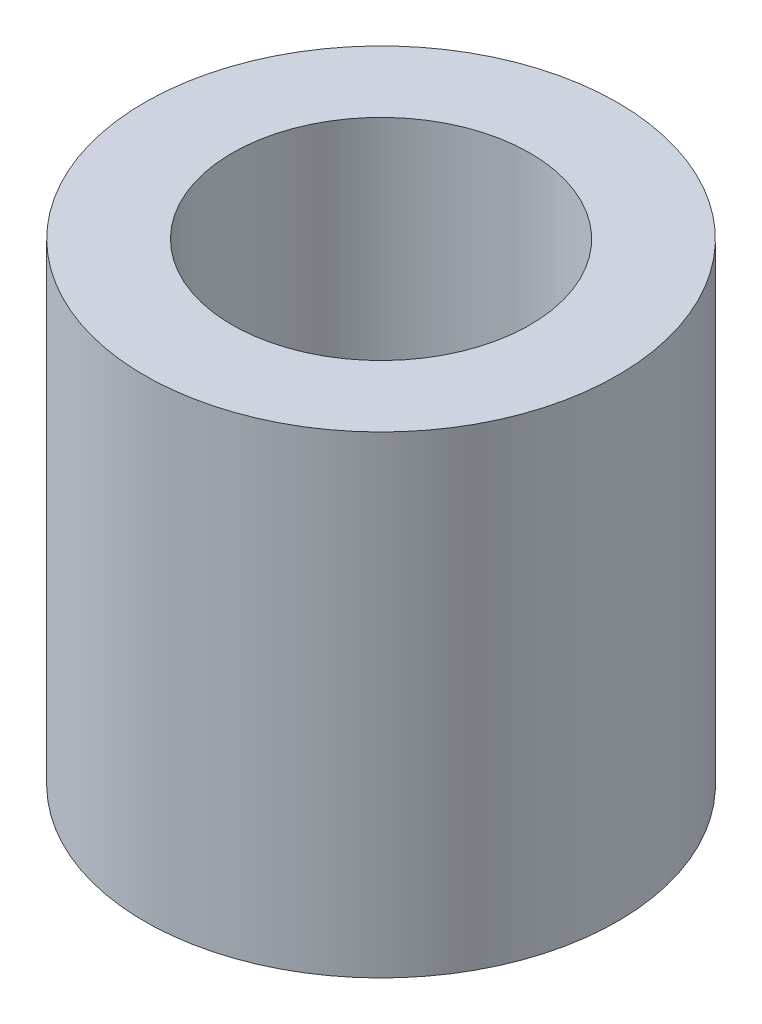
SolidWorks part; units mm, degrees
ref_plane "Front Plane" through (0, 0, 0) normal (0, 0, 1) x (1, 0, 0)
ref_plane "Top Plane" through (0, 0, 0) normal (0, 1, 0) x (1, 0, 0)
ref_plane "Right Plane" through (0, 0, 0) normal (1, 0, 0) x (0, 0, -1)
sketch "Sketch1" plane through (0, 0, 0) normal (0, 0, 1) x (1, 0, 0)
  line L0 (0, 0) -> (0, 6.7287) construction
  line L2 (-2, 0) -> (-3.175, 0)
  line L3 (-2, 0) -> (-2, 6.35)
  line L4 (-2, 6.35) -> (-3.175, 6.35)
  line L5 (-3.175, 0) -> (-3.175, 6.35)
  dimension "D1" = 6.35
  dimension "D2" = 6.35
  dimension "D3" = 4
revolve "Revolve1" add sketch "Sketch1" angle 360 about L0
